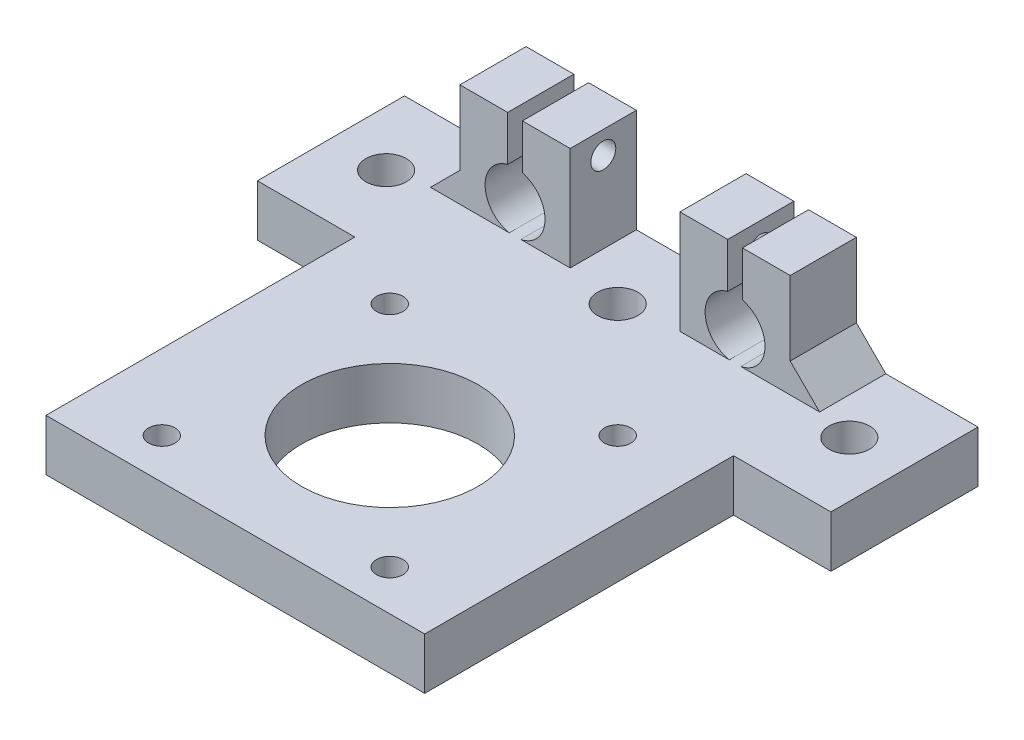
SolidWorks part; units mm, degrees
ref_plane "Front Plane" through (0, 0, 0) normal (0, 0, 1) x (1, 0, 0)
ref_plane "Top Plane" through (0, 0, 0) normal (0, 1, 0) x (1, 0, 0)
ref_plane "Right Plane" through (0, 0, 0) normal (1, 0, 0) x (0, 0, -1)
sketch "Sketch1" plane through (0, 0, 0) normal (0, 1, 0) x (1, 0, 0)
  line L1 (21, 21) -> (-21, 21)
  line L2 (21, 21) -> (21, -21)
  line L3 (21, -21) -> (-21, -21)
  line L4 (-21, 21) -> (-21, -21)
  line L5 (0, -21) -> (0, 21) construction
  line L6 (21, 0) -> (-21, 0) construction
  line L7 (15.5, 15.5) -> (-15.5, 15.5) construction
  line L8 (15.5, 15.5) -> (15.5, -15.5) construction
  line L9 (15.5, -15.5) -> (-15.5, -15.5) construction
  line L10 (-15.5, 15.5) -> (-15.5, -15.5) construction
  line L11 (0, -15.5) -> (0, 15.5) construction
  line L12 (15.5, 0) -> (-15.5, 0) construction
  point P0 (0, 0)
  point P4 (0, 0)
  dimension "D1" = 31
  dimension "D2" = 31
  dimension "D3" = 42
extrude "Boss-Extrude1" add sketch "Sketch1" along normal blind 3
hole_wizard "M3 Clearance Hole1" positions "Sketch2" profile "Sketch3" hole size "M3" standard "ANSI Metric" end condition through all
sketch "Sketch2" plane through (0, 3, 0) normal (0, 1, 0) x (1, 0, 0)
  point P0 (-15.5, 15.5)
  point P3 (-15.5, -15.5)
  point P6 (15.5, -15.5)
  point P9 (15.5, 15.5)
sketch "Sketch3" plane through (-15.5, 3, -15.5) normal (1, 0, 0) x (0, 0, 1)
  line L0 (0, 0) -> (0, 3)
  line L1 (0, 3) -> (1.8, 3)
  line L2 (1.8, 3) -> (1.8, 0)
  line L5 (1.8, 0) -> (0, 0)
  line L11 (0, -6.35) -> (0, 107.95) construction
  dimension "Thru Hole Dia." = 3.6
  dimension "Thru Hole Depth" = 3
sketch "Sketch4" plane through (0, 3, 0) normal (0, 1, 0) x (1, 0, 0)
  line L0 (21, 0) -> (-21, 0) construction
  circle A0 centre (0, 0) radius 12
  dimension "D1" = 24
extrude "Cut-Extrude1" cut sketch "Sketch4" against normal through all
sketch "Sketch5" plane through (0, 0, 0) normal (0, 0, 1) x (1, 0, 0)
  circle A0 centre (-14.96, 7) radius 4
  dimension "D3" = 8
  dimension "D1" = 7
  dimension "D2" = 14.96
extrude "Boss-Extrude2" add sketch "Sketch5" against normal blind 20 from offset 34 separate body offset against normal yes
sketch "Sketch6" plane through (0, 0, 0) normal (0, 1, 0) x (1, 0, 0)
  line L1 (-21, 21) -> (21, 21)
  line L2 (-21, 21) -> (-21, 41)
  line L3 (-21, 41) -> (21, 41)
  line L4 (21, 21) -> (21, 41)
  line L5 (0, 41) -> (0, 21) construction
  line L6 (-21, 31) -> (21, 31) construction
  point P116 (0, 31)
  dimension "D1" = 20
extrude "Boss-Extrude3" add sketch "Sketch6" along normal up to surface (3 mm away) up to face at (0, 3, 12)
sketch "Sketch7" plane through (0, 0, 0) normal (0, 1, 0) x (1, 0, 0)
  line L0 (-21, 41) -> (21, 41) construction
  line L1 (-21, -21) -> (-25.75, -21)
  line L2 (-21, -21) -> (-21, 41)
  line L3 (-21, 41) -> (-25.75, 41)
  line L4 (-25.75, -21) -> (-25.75, 41)
  line L5 (-23.375, 41) -> (-23.375, -21) construction
  line L6 (-21, 10) -> (-25.75, 10) construction
  line L7 (21, -21) -> (21, 41) construction
  line L9 (21, 41) -> (25.75, 41)
  line L10 (21, 41) -> (21, -21)
  line L11 (21, -21) -> (25.75, -21)
  line L12 (25.75, 41) -> (25.75, -21)
  line L13 (23.375, -21) -> (23.375, 41) construction
  line L14 (21, 10) -> (25.75, 10) construction
  point P192 (-23.375, 10)
  point P266 (23.375, 10)
  dimension "D1" = 46.75
extrude "Boss-Extrude4" add sketch "Sketch7" along normal up to surface (3 mm away) up to face at (0, 3, 12)
sketch "Sketch8" plane through (0, 0, -34) normal (0, 0, 1) x (1, 0, 0)
  line L0 (-25.75, 3) -> (25.75, 3) construction
  line L1 (-22.46, 3) -> (-7.46, 3)
  line L2 (-22.46, 3) -> (-22.46, 17.075)
  line L3 (-22.46, 17.075) -> (-7.46, 17.075)
  line L4 (-7.46, 3) -> (-7.46, 17.075)
  line L5 (-14.96, 17.075) -> (-14.96, 3) construction
  line L6 (-22.46, 10.0375) -> (-7.46, 10.0375) construction
  line L8 (-15.96, 17.075) -> (-13.96, 17.075)
  line L9 (-15.96, 17.075) -> (-15.96, 10.0375)
  line L10 (-15.96, 10.0375) -> (-13.96, 10.0375)
  line L11 (-13.96, 17.075) -> (-13.96, 10.0375)
  line L12 (-14.96, 10.0375) -> (-14.96, 17.075) construction
  line L13 (-15.96, 13.5563) -> (-13.96, 13.5563) construction
  circle A0 centre (-14.96, 7) radius 4.075
  point P295 (-14.96, 10.0375)
  point P375 (-14.96, 13.5563)
  circle M6 centre (-14.96, 7) radius 4
  dimension "D2" = 8.15
  dimension "D4" = 6
  dimension "D1" = 15
  dimension "D3" = 2
extrude "Boss-Extrude5" add sketch "Sketch8" against normal up to surface (7 mm away) and the other way blind 2 contours L9 L3 L2 L1 M6 | L3 L11 L1 L4 M6
hole_wizard "M3 Clearance Hole2" positions "Sketch9" profile "Sketch10" hole size "M3" standard "ANSI Metric"
sketch "Sketch9" plane through (-7.46, 0, 0) normal (1, 0, 0) x (0, 0, -1)
  line L0 (36.5, 14.0127) -> (32, 14.0127) construction
  line L1 (32, 3) -> (32, 17.075) construction
  line L3 (32, 17.075) -> (32, 10.9504) construction
  line L4 (36.5, 17.075) -> (36.5, 14.0127) construction
  line L5 (41, 17.075) -> (32, 17.075) construction
  point P0 (36.5, 14.0127)
sketch "Sketch10" plane through (-7.46, 14.0127, -36.5) normal (0, 1, 0) x (0, 0, -1)
  line L0 (0, 0) -> (0, 7.3715)
  line L1 (0, 7.3715) -> (1.7, 6.35)
  line L2 (1.7, 6.35) -> (1.7, 0)
  line L5 (1.7, 0) -> (0, 0)
  line L10 (0, 7.3715) -> (-1.7, 6.35) construction
  line L11 (0, -6.35) -> (0, 107.95) construction
  dimension "Hole Dia." = 3.4
  dimension "Hole Depth" = 6.35
  dimension "Drill Angle" = 118
mirror "Mirror2" about plane through (0, 0, 0) normal (1, 0, 0) of "Boss-Extrude5", "M3 Clearance Hole2"
mirror "Mirror1" [suppressed] about plane through (0, 0, 0) normal (1, 0, 0)
delete or keep bodies "Body-Delete/Keep 1" [suppressed] type delete bodies bodies 108 104
delete or keep bodies "Body-Delete/Keep 2" type delete bodies bodies 104
sketch "Sketch13" plane through (0, 3, 0) normal (0, 1, 0) x (1, 0, 0)
  line L0 (-25.75, -21) -> (-25.75, 41) construction
  line L1 (-25.75, 21) -> (-39, 21)
  line L2 (-25.75, 21) -> (-25.75, 41)
  line L3 (-25.75, 41) -> (-39, 41)
  line L4 (-39, 21) -> (-39, 41)
  line L5 (-32.375, 41) -> (-32.375, 21) construction
  line L6 (-25.75, 31) -> (-39, 31) construction
  line L7 (25.75, 41) -> (25.75, -21) construction
  line L8 (25.75, 21) -> (39, 21)
  line L9 (25.75, 21) -> (25.75, 41)
  line L10 (25.75, 41) -> (39, 41)
  line L11 (39, 21) -> (39, 41)
  line L12 (32.375, 41) -> (32.375, 21) construction
  line L13 (25.75, 31) -> (39, 31) construction
  point P120 (-32.375, 31)
  point P183 (32.375, 31)
  dimension "D1" = 20
  dimension "D2" = 78
extrude "Boss-Extrude6" add sketch "Sketch13" against normal blind 3
hole_wizard "M5 Clearance Hole1" positions "Sketch11" profile "Sketch12" hole size "M5" standard "ANSI Metric" end condition through all
sketch "Sketch11" plane through (0, 3, 0) normal (0, 1, 0) x (1, 0, 0)
  line L0 (-31.5, 31) -> (31.5, 31) construction
  line L3 (0, 31) -> (0, 41) construction
  line L6 (-7.46, 41) -> (7.46, 41) construction
  point P0 (0, 31)
  point P2 (-31.5, 31)
  point P4 (31.5, 31)
  dimension "D1" = 63
  dimension "D2" = 10
sketch "Sketch12" plane through (0, 3, -31) normal (1, 0, 0) x (0, 0, 1)
  line L0 (0, 0) -> (0, 3)
  line L1 (0, 3) -> (2.75, 3)
  line L2 (2.75, 3) -> (2.75, 0)
  line L5 (2.75, 0) -> (0, 0)
  line L11 (0, -6.35) -> (0, 107.95) construction
  dimension "Thru Hole Dia." = 5.5
  dimension "Thru Hole Depth" = 3
chamfer "Chamfer1" distance 4 angle 45 2 edges at (22.46, 3, -36.5) (-22.46, 3, -36.5)
sketch "Sketch14" plane through (0, 3, 0) normal (0, 1, 0) x (1, 0, 0)
  circle A0 centre (-31.5, 31) radius 4.35
  circle A1 centre (0, 31) radius 4.35
  circle A2 centre (31.5, 31) radius 4.35
  dimension "D1" = 8.7
other "Move Face1" face at (0, 0, -28.25) parameters "D1"=4
